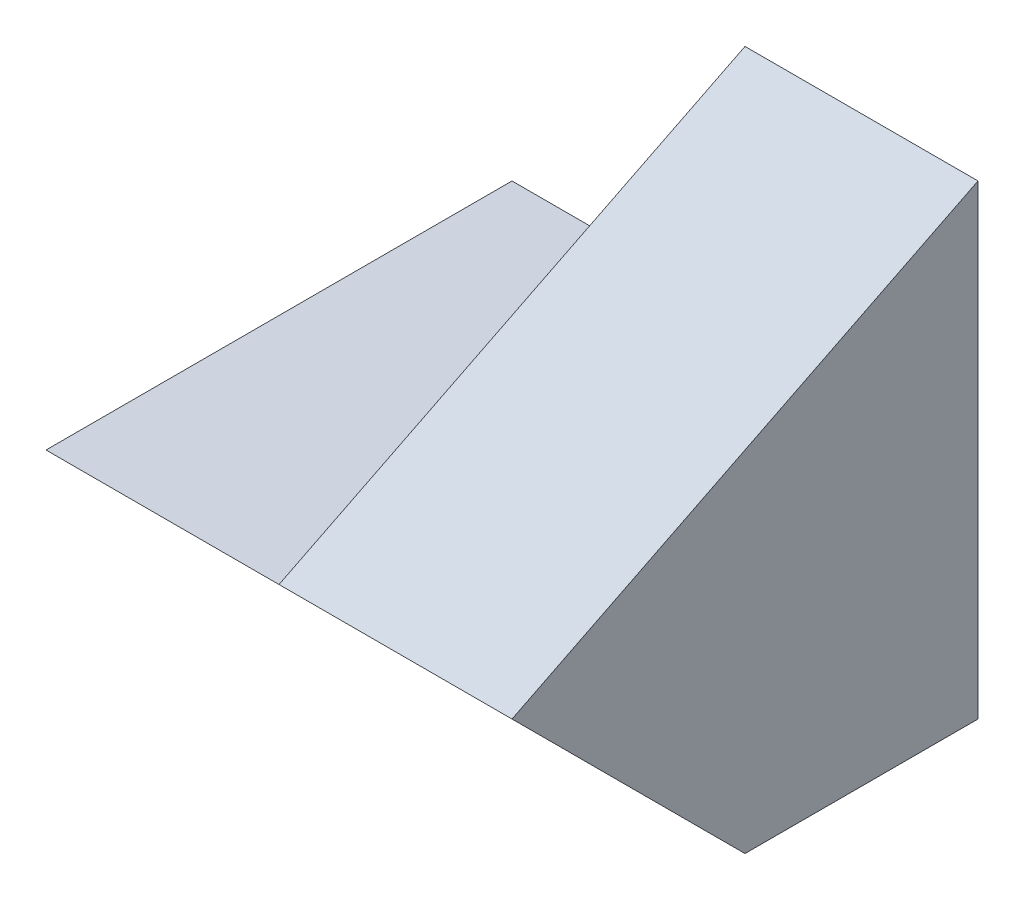
SolidWorks part; units mm, degrees
ref_plane "Front Plane" through (0, 0, 0) normal (0, 0, 1) x (1, 0, 0)
ref_plane "Top Plane" through (0, 0, 0) normal (0, 1, 0) x (1, 0, 0)
ref_plane "Right Plane" through (0, 0, 0) normal (1, 0, 0) x (0, 0, -1)
sketch "Sketch1" plane through (0, 0, 0) normal (0, 0, 1) x (1, 0, 0)
  line L1 (0, 0) -> (40, 0)
  line L2 (0, 0) -> (0, 40)
  line L3 (0, 40) -> (40, 40)
  line L4 (40, 0) -> (40, 40)
  dimension "D1" = 40
  dimension "D2" = 40
extrude "Boss-Extrude1" add sketch "Sketch1" along normal blind 40
sketch "Sketch2" plane through (0, 0, 40) normal (0, 0, 1) x (1, 0, 0)
  line L1 (0, 40) -> (20, 40)
  line L2 (0, 40) -> (0, 20)
  line L3 (0, 20) -> (20, 20)
  line L4 (20, 40) -> (20, 20)
  dimension "D1" = 20
  dimension "D2" = 20
extrude "Cut-Extrude1" cut sketch "Sketch2" against normal blind 40
sketch "Sketch3" plane through (20, 0, 0) normal (-1, 0, 0) x (0, 0, 1)
  line L0 (0, 40) -> (40, 20)
  line L1 (40, 20) -> (40, 40)
  line L2 (40, 40) -> (0, 40)
extrude "Cut-Extrude2" cut sketch "Sketch3" against normal blind 40
sketch "Sketch4" plane through (0, 0, 0) normal (-1, 0, 0) x (0, 0, 1)
  line L0 (40, 20) -> (20, 0)
  line L1 (40, 0) -> (0, 0) construction
  line L2 (20, 0) -> (40, 0)
  line L3 (40, 0) -> (40, 20)
extrude "Cut-Extrude3" cut sketch "Sketch4" against normal blind 40
